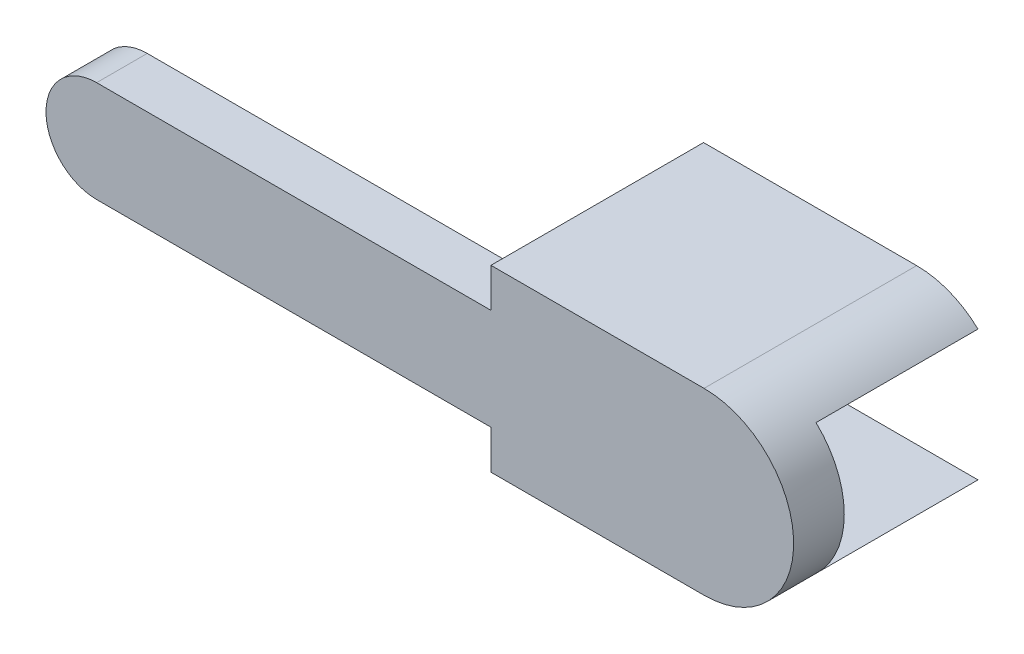
SolidWorks part; units mm, degrees
ref_plane "Front" through (0, 0, 0) normal (0, 0, 1) x (1, 0, 0)
ref_plane "Top" through (0, 0, 0) normal (0, 1, 0) x (1, 0, 0)
ref_plane "Right" through (0, 0, 0) normal (1, 0, 0) x (0, 0, -1)
sketch "Sketch1" plane through (0, 0, 0) normal (0, 0, 1) x (1, 0, 0)
  line L0 (0, 0) -> (60, 0) construction
  line L1 (0, 5) -> (60, 5)
  line L2 (0, -5) -> (60, -5)
  arc A0 (0, 5) -> (0, -5) centre (0, 0) ccw
  arc A1 (60, -5) -> (60, 5) centre (60, 0) ccw
  point P3 (30, 0)
  dimension "D2" = 10
  dimension "D1" = 60
extrude "Boss-Extrude1" add sketch "Sketch1" along normal blind 5 contours A0 L2 A1 L1
sketch "Sketch2" plane through (0, 0, 0) normal (0, 0, -1) x (-1, 0, 0)
  circle A0 centre (0, 0) radius 2.35
  dimension "D1" = 4.7
extrude "Cut-Extrude1" cut sketch "Sketch2" against normal blind 3 contours A0
sketch "Sketch3" plane through (0, 0, 5) normal (0, 0, 1) x (1, 0, 0)
  line L0 (38.95, -6.35) -> (38.95, 6.35) construction
  line L1 (38.95, -6.35) -> (38.95, 6.35)
  line L2 (38.95, 6.35) -> (38.95, 8.85)
  line L3 (38.95, 8.85) -> (60, 8.85)
  line L4 (43.55, 6.35) -> (66.35, 6.35) construction
  line L5 (43.55, 6.35) -> (66.35, 6.35) construction
  line L6 (38.95, 0) -> (68.85, 0) construction
  line L7 (38.95, -8.85) -> (60, -8.85)
  line L8 (38.95, -6.35) -> (38.95, -8.85)
  arc A0 (60, 8.85) -> (60, -8.85) centre (60, 0) cw
  dimension "D1" = 2.5
extrude "Boss-Extrude3" add sketch "Sketch3" against normal up to surface (5 mm away) contours L3 A0 L7 L8 L1 L2 up to face at (-2.35, 0, 0)
sketch "Sketch4" plane through (0, 0, 0) normal (0, 0, -1) x (-1, 0, 0)
  line L0 (-60, 8.85) -> (-38.95, 8.85) construction
  line L1 (-60, -8.85) -> (-38.95, -8.85) construction
  line L2 (-60, 8.85) -> (-38.95, 8.85)
  line L3 (-60, -8.85) -> (-38.95, -8.85)
  line L4 (-38.95, -5) -> (-38.95, -8.85) construction
  line L5 (-38.95, 8.85) -> (-38.95, 5) construction
  line L6 (-38.95, -5) -> (-38.95, -8.85)
  line L7 (-38.95, 8.85) -> (-38.95, 5)
  line L8 (-38.95, -5) -> (-38.95, 5)
  line L11 (-66.0597, -6.45) -> (-43.45, -6.45)
  line L12 (-43.45, -6.45) -> (-43.45, 6.45)
  line L13 (-43.45, 6.45) -> (-66.0597, 6.45)
  line L18 (-43.55, -6.35) -> (-43.55, 6.35)
  line L19 (-66.35, -6.35) -> (-43.55, -6.35)
  line L20 (-66.35, 6.35) -> (-66.35, -6.35)
  line L21 (-43.55, 6.35) -> (-66.35, 6.35)
  line L22 (-43.55, -6.35) -> (-43.55, 6.35) construction
  line L23 (-66.35, -6.35) -> (-43.55, -6.35) construction
  line L24 (-66.35, 6.35) -> (-66.35, -6.35) construction
  line L25 (-43.55, 6.35) -> (-66.35, 6.35) construction
  arc A0 (-60, -8.85) -> (-66.0597, -6.45) centre (-60, 0) cw
  arc A1 (-60, 8.85) -> (-60, -8.85) centre (-60, 0) ccw construction
  arc A2 (-60, 8.85) -> (-66.0597, 6.45) centre (-60, 0) ccw
  dimension "D1" = 0
  dimension "D2" = 0.1
  dimension "D3" = 0.1
  dimension "D4" = 0.1
extrude "Boss-Extrude4" add sketch "Sketch4" along normal up to surface (16 mm away)
sketch "Sketch5" plane through (0, 0, -16) normal (0, 0, -1) x (-1, 0, 0)
  circle A4 centre (-41.25, 0) radius 1.025
  circle A5 centre (-41.25, 0) radius 1.025
  dimension "D1" = 0.1
extrude "Cut-Extrude2" cut sketch "Sketch5" against normal blind 5
